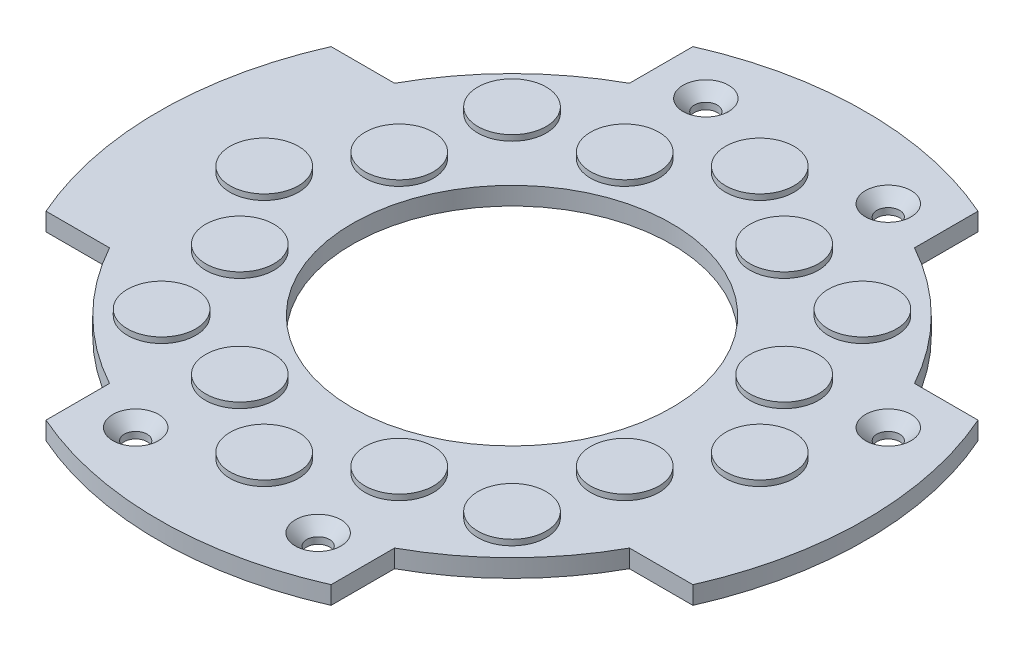
SolidWorks part; units mm, degrees
material "Custom Plastic"
ref_plane "Front Plane" through (0, 0, 0) normal (0, 0, 1) x (1, 0, 0)
ref_plane "Top Plane" through (0, 0, 0) normal (0, 1, 0) x (1, 0, 0)
ref_plane "Right Plane" through (0, 0, 0) normal (1, 0, 0) x (0, 0, -1)
sketch "Sketch1" plane through (0, 0, 0) normal (0, 1, 0) x (1, 0, 0)
  line L0 (-6.25, 14.1841) -> (-6.25, 11.399)
  line L1 (0, 15.5) -> (0, 0) construction
  line L2 (0, 0) -> (-10.9602, 10.9602) construction
  line L3 (-14.1841, 6.25) -> (-11.399, 6.25)
  line L4 (6.25, 14.1841) -> (6.25, 11.399)
  line L5 (14.1841, 6.25) -> (11.399, 6.25)
  line L6 (0, 0) -> (15.5, 0) construction
  line L7 (14.1841, -6.25) -> (11.399, -6.25)
  line L8 (6.25, -14.1841) -> (6.25, -11.399)
  line L9 (-6.25, -14.1841) -> (-6.25, -11.399)
  line L10 (-14.1841, -6.25) -> (-11.399, -6.25)
  circle A0 centre (0, 0) radius 13 construction
  circle A1 centre (0, 0) radius 15.5 construction
  arc A2 (-6.25, 14.1841) -> (6.25, 14.1841) centre (0, 0) cw
  arc A3 (-6.25, 11.399) -> (-11.399, 6.25) centre (0, 0) ccw
  arc A4 (-14.1841, 6.25) -> (-14.1841, -6.25) centre (0, 0) ccw
  arc A5 (6.25, 11.399) -> (11.399, 6.25) centre (0, 0) cw
  arc A6 (14.1841, 6.25) -> (14.1841, -6.25) centre (0, 0) cw
  arc A7 (6.25, -11.399) -> (11.399, -6.25) centre (0, 0) ccw
  arc A8 (-6.25, -14.1841) -> (6.25, -14.1841) centre (0, 0) ccw
  arc A9 (-6.25, -11.399) -> (-11.399, -6.25) centre (0, 0) cw
  circle A10 centre (0, 0) radius 7
  dimension "D1" = 31
  dimension "D2" = 26
  dimension "D5" = 14
  dimension "D3" = 6.25
  dimension "D4" = 45
extrude "Boss-Extrude1" add sketch "Sketch1" along normal blind 0.7874
sketch "Sketch2" plane through (0, 0.7874, 0) normal (0, 1, 0) x (1, 0, 0)
  line L0 (0, 0) -> (-15.5, 0) construction
  line L2 (-9.1924, 9.1924) -> (0, 0) construction
  line L4 (0, 0) -> (-14.3201, 5.9316) construction
  line L11 (0, 0) -> (0, 15.5) construction
  circle A0 centre (0, 10.865) radius 1.5
  circle A1 centre (-3.4958, 8.4396) radius 1.5
  arc A2 (-14.1841, 6.25) -> (-14.1841, -6.25) centre (0, 0) ccw construction
  circle A3 centre (0, 0) radius 7 construction
  arc A4 (-6.25, 11.399) -> (-11.399, 6.25) centre (0, 0) ccw construction
  circle A5 centre (-10.865, 0) radius 1.5
  circle A6 centre (-8.4396, 3.4958) radius 1.5
  circle A7 centre (-7.6827, 7.6827) radius 1.5
  circle A8 centre (0, -10.865) radius 1.5
  circle A9 centre (-3.4958, -8.4396) radius 1.5
  circle A10 centre (-7.6827, -7.6827) radius 1.5
  circle A11 centre (-8.4396, -3.4958) radius 1.5
  circle A12 centre (3.4958, 8.4396) radius 1.5
  circle A13 centre (7.6827, 7.6827) radius 1.5
  circle A14 centre (8.4396, 3.4958) radius 1.5
  arc A15 (6.25, 14.1841) -> (-6.25, 14.1841) centre (0, 0) ccw construction
  circle A16 centre (10.865, 0) radius 1.5
  arc A17 (11.399, 6.25) -> (11.399, -6.25) centre (0, 0) cw construction
  circle A18 centre (8.4396, -3.4958) radius 1.5
  circle A19 centre (7.6827, -7.6827) radius 1.5
  circle A20 centre (3.4958, -8.4396) radius 1.5
  arc A36 (-11.399, 6.25) -> (-11.399, -6.25) centre (0, 0) ccw construction
  point P0 (-13, 0)
  point P11 (-7, 0)
  point P19 (-4.9497, 4.9497)
  point P20 (-12.365, 0)
  point P24 (-7.5, 0)
  point P25 (-8.5, 0)
  point P28 (-8.7434, 8.7434)
  point P56 (-6.4672, 2.6788)
  point P94 (-7.0538, 2.9218)
  dimension "D2" = 3
  dimension "padRadius" = 1.5
  dimension "D7" = 0.635
  dimension "D1" = 0.635
  dimension "D3" = 0.5
  dimension "D4" = 1
  dimension "D5" = 22.5
  dimension "D8" = 0.635
extrude "Boss-Extrude2" add sketch "Sketch2" along normal blind 0.25
sketch "Sketch3" plane through (0, 0.7874, 0) normal (0, 1, 0) x (1, 0, 0)
  line L0 (0, 0) -> (0, 15.5) construction
  line L1 (0, 0) -> (15.5, 0) construction
  line L2 (-4, 12.5) -> (0, 0) construction
  line L3 (0, 0) -> (12.5, 4) construction
  circle A0 centre (-4, 12.5) radius 0.5
  arc A1 (6.25, 14.1841) -> (-6.25, 14.1841) centre (0, 0) ccw construction
  arc A2 (14.1841, -6.25) -> (14.1841, 6.25) centre (0, 0) ccw construction
  circle A3 centre (4, 12.5) radius 0.5
  circle A4 centre (4, -12.5) radius 0.5
  circle A5 centre (-4, -12.5) radius 0.5
  circle A6 centre (12.5, 4) radius 0.5
  dimension "D2" = 1
  dimension "D1" = 12.5
  dimension "D3" = 4
  dimension "D5" = 90
  dimension "D4" = 2
extrude "Cut-Extrude1" cut sketch "Sketch3" against normal through all
chamfer "Chamfer1" distance 0.5 angle 45 5 edges at (12.5, 0.7874, -4.5) (4, 0.7874, 13) (-4, 0.7874, 12) (4, 0.7874, -13) (-4, 0.7874, -12)
equation "\"D2@Sketch2\" = \"padRadius\" * 2"
